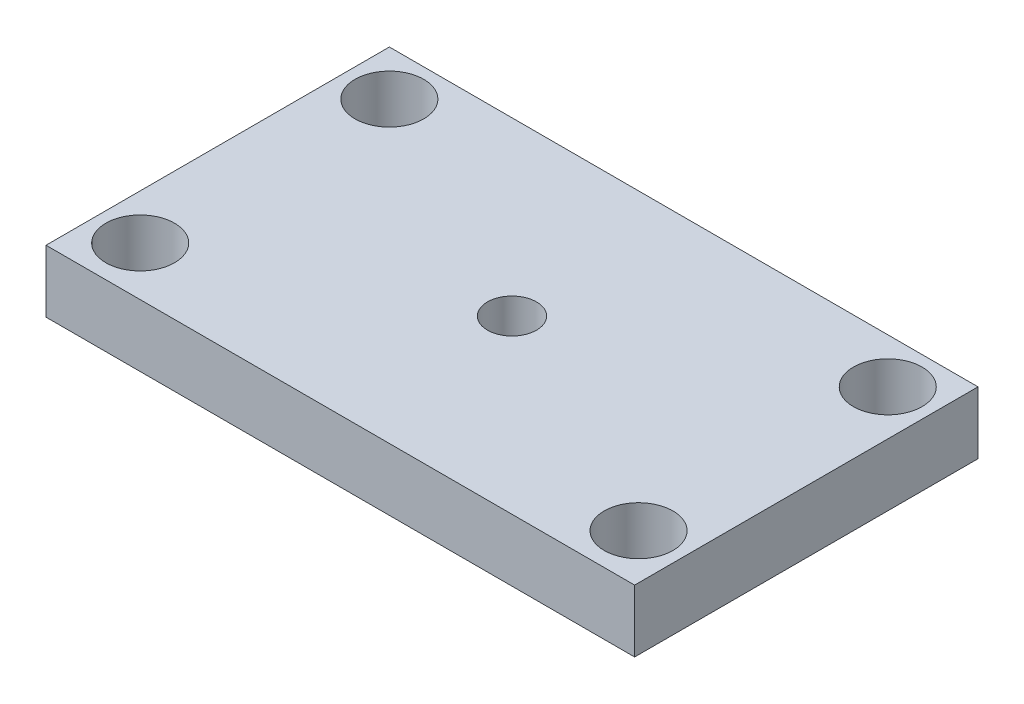
SolidWorks part; units mm, degrees
ref_plane "Front Plane" through (0, 0, 0) normal (0, 0, 1) x (1, 0, 0)
ref_plane "Top Plane" through (0, 0, 0) normal (0, 1, 0) x (1, 0, 0)
ref_plane "Right Plane" through (0, 0, 0) normal (1, 0, 0) x (0, 0, -1)
sketch "Sketch1" plane through (0, 0, 0) normal (0, 1, 0) x (1, 0, 0)
  line L0 (4.6, 30.4) -> (0, 30.4) construction
  line L1 (0, 0) -> (60, 0)
  line L2 (0, 0) -> (0, 35)
  line L3 (0, 35) -> (60, 35)
  line L4 (60, 0) -> (60, 35)
  line L5 (4.6, 30.4) -> (55.4, 30.4) construction
  line L6 (4.6, 30.4) -> (4.6, 5) construction
  line L7 (4.6, 5) -> (55.4, 5) construction
  line L8 (55.4, 30.4) -> (55.4, 5) construction
  line L9 (4.6, 30.4) -> (4.6, 35) construction
  circle A0 centre (4.6, 30.4) radius 3.5
  circle A1 centre (55.4, 30.4) radius 3.5
  circle A2 centre (4.6, 5) radius 3.5
  circle A3 centre (55.4, 5) radius 3.5
  circle A4 centre (30, 17.5) radius 2.5
  point P13 (30, 30.4)
  point P14 (30, 35)
  point P20 (60, 17.5)
  dimension "D5" = 7
  dimension "D6" = 5
  dimension "D1" = 60
  dimension "D2" = 35
  dimension "D3" = 50.8
  dimension "D4" = 25.4
extrude "Boss-Extrude1" add sketch "Sketch1" along normal blind 6.35
